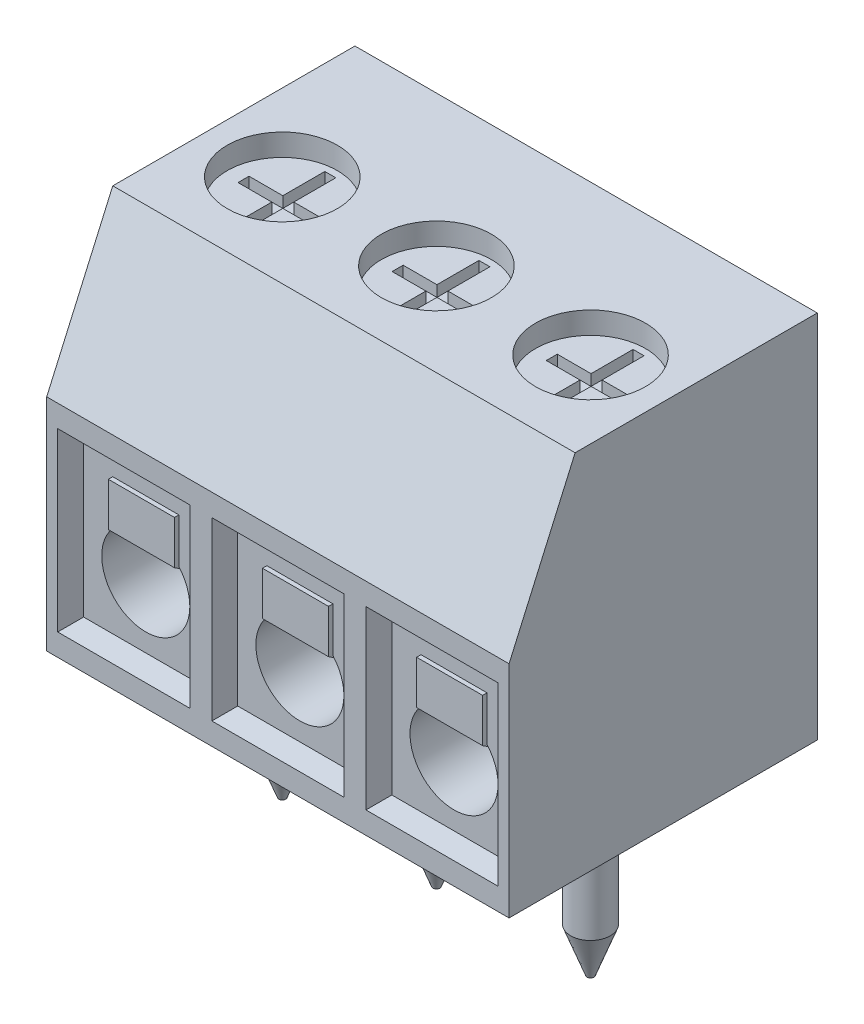
SolidWorks part; units mm, degrees
ref_plane "Front Plane" through (0, 0, 0) normal (0, 0, 1) x (1, 0, 0)
ref_plane "Top Plane" through (0, 0, 0) normal (0, 1, 0) x (1, 0, 0)
ref_plane "Right Plane" through (0, 0, 0) normal (1, 0, 0) x (0, 0, -1)
sketch "Sketch1" plane through (0, 0, 0) normal (1, 0, 0) x (0, 0, -1)
  line L0 (0, 5) -> (1.5, 8.4)
  line L1 (0, 0) -> (7, 0)
  line L2 (0, 0) -> (0, 5)
  line L3 (1.5, 8.4) -> (7, 8.4)
  line L4 (7, 0) -> (7, 8.4)
  dimension "D1" = 7
  dimension "D2" = 8.4
  dimension "D3" = 5
  dimension "D4" = 5.5
extrude "Boss-Extrude1" add sketch "Sketch1" along normal blind 10.5 contours L0 L3 L4 L1 L2
sketch "Sketch2" plane through (0, 8.4, 0) normal (0, 1, 0) x (1, 0, 0)
  line L0 (10.5, 7) -> (0, 7) construction
  line L1 (0, 1.5) -> (0, 7) construction
  circle A0 centre (1.75, 3.6) radius 1.25
  dimension "D1" = 2.5
  dimension "D2" = 3.4
  dimension "D3" = 1.75
extrude "Cut-Extrude1" cut sketch "Sketch2" against normal blind 0.5
sketch "Sketch3" plane through (0, 0, 0) normal (0, 0, 1) x (1, 0, 0)
  line L0 (0, 0) -> (0, 5) construction
  line L1 (0.25, 0.5) -> (3.25, 0.5)
  line L2 (0.25, 0.5) -> (0.25, 4.5)
  line L3 (0.25, 4.5) -> (3.25, 4.5)
  line L4 (3.25, 0.5) -> (3.25, 4.5)
  line L5 (10.5, 0) -> (0, 0) construction
  line L6 (10.5, 5) -> (0, 5) construction
  dimension "D1" = 0.25
  dimension "D2" = 3
  dimension "D3" = 0.5
  dimension "D4" = 0.5
extrude "Cut-Extrude2" cut sketch "Sketch3" against normal blind 0.5 draft 10 contours L3 L4 L1 L2
sketch "Sketch4" plane through (0, 0, -0.5) normal (0, 0, 1) x (1, 0, 0)
  line L0 (1.75, 0.5882) -> (1.75, 4.4118) construction
  line L1 (0.3382, 0.5882) -> (3.1618, 0.5882) construction
  line L2 (0.3382, 4.4118) -> (3.1618, 4.4118) construction
  line L3 (0.25, 0.5) -> (3.25, 0.5) construction
  circle A0 centre (1.75, 2) radius 1
  point P8 (1.75, 0.5)
  dimension "D1" = 2
  dimension "D2" = 1.5
extrude "Cut-Extrude3" cut sketch "Sketch4" against normal blind 6
ref_plane "Plane1" through (1.75, 0, 0) normal (1, 0, 0) x (0, 0, -1)
sketch "Sketch6" plane through (0, 0, 0) normal (0, -1, 0) x (1, 0, 0)
  line L0 (1.75, -3.85) -> (1.75, 3.85) construction
  line L1 (10.5, -7) -> (0, -7) construction
  circle A0 centre (1.75, -3.6) radius 0.45
  dimension "D1" = 0.9
  dimension "D2" = 3.4
extrude "Boss-Extrude3" add sketch "Sketch6" along normal blind 3.8
chamfer "Chamfer1" distance 1 angle 20.4 1 edges at (1.75, -3.8, -4.05)
sketch "Sketch7" plane through (1.75, 0, 0) normal (1, 0, 0) x (0, 0, -1)
  line L0 (0.5, 3.6787) -> (0.5, 2.7432)
  line L1 (0.5, 0.5882) -> (0.5, 4.4118) construction
  line L2 (0.5, 2.7432) -> (1.8997, 1.8322)
  line L3 (1.8997, 1.8322) -> (5.8881, 1.4383)
extrude "Extrude-Thin1" add sketch "Sketch7" along normal mid plane 1.5 thin
sketch "Sketch8" plane through (0, 7.9, 0) normal (0, 1, 0) x (1, 0, 0)
  line L0 (1.75, 4.6908) -> (1.75, 2.5325)
  line L1 (1.75, -3.85) -> (1.75, 3.85) construction
  line L2 (0.858, 3.6116) -> (2.7323, 3.6116)
extrude "Cut-Extrude-Thin1" cut sketch "Sketch8" against normal mid plane 0.5 thin thin type mid plane wall 0.25
pattern_linear "LPattern1" count 3 spacing 3.5 along (1, 0, 0) of "Cut-Extrude1", "Cut-Extrude2", "Cut-Extrude3", "Boss-Extrude3", "Chamfer1", "Extrude-Thin1", "Cut-Extrude-Thin1"
